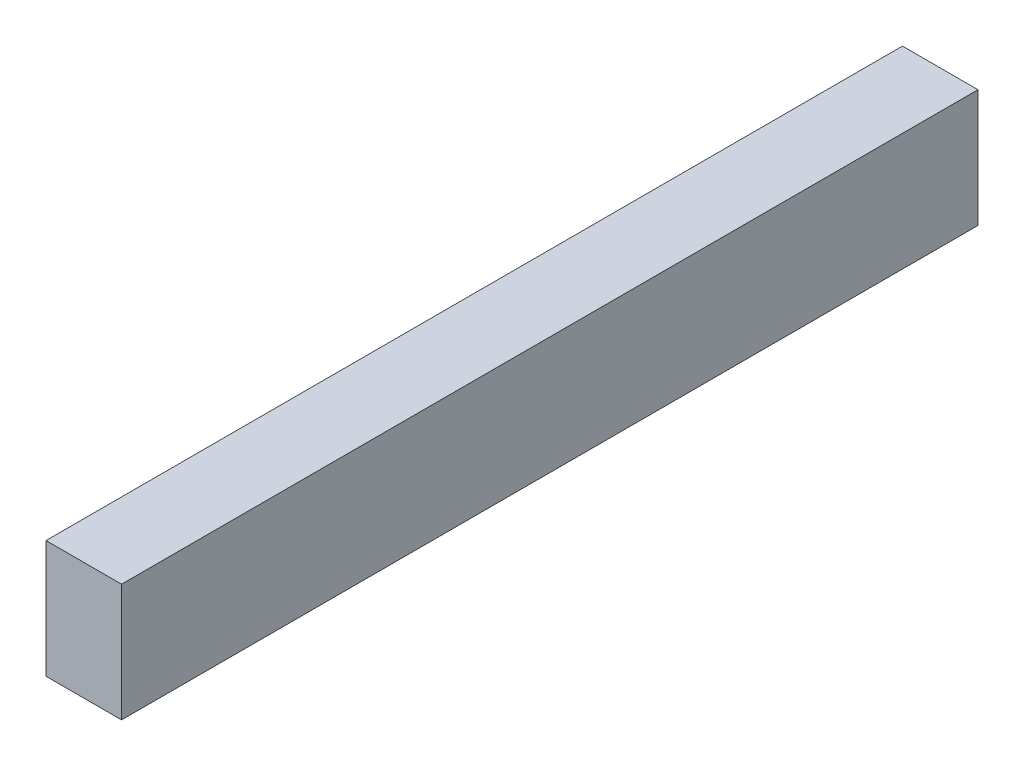
SolidWorks part; units mm, degrees
material "Pine"
ref_plane "Front Plane" through (0, 0, 0) normal (0, 0, 1) x (1, 0, 0)
ref_plane "Top Plane" through (0, 0, 0) normal (0, 1, 0) x (1, 0, 0)
ref_plane "Right Plane" through (0, 0, 0) normal (1, 0, 0) x (0, 0, -1)
sketch "Sketch1" plane through (0, 0, 0) normal (0, 0, 1) x (1, 0, 0)
  line L1 (0, 0) -> (45, 0)
  line L2 (0, 0) -> (0, -70)
  line L3 (0, -70) -> (45, -70)
  line L4 (45, 0) -> (45, -70)
  dimension "D1" = 45
  dimension "D2" = 70
extrude "Boss-Extrude1" add sketch "Sketch1" along normal blind 510
